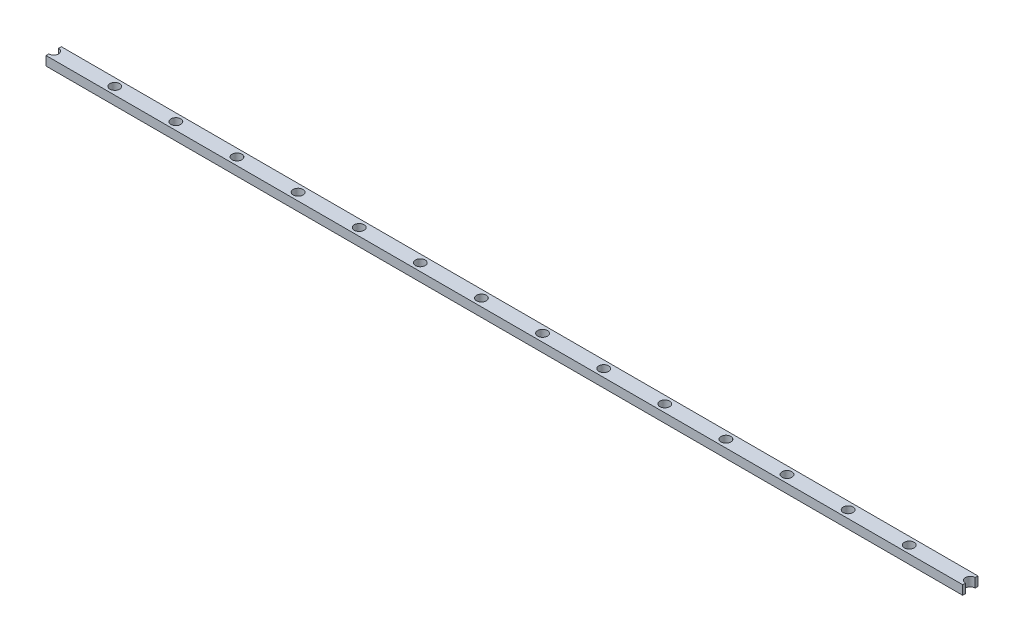
SolidWorks part; units mm, degrees
ref_plane "Front Plane" through (0, 0, 0) normal (0, 0, 1) x (1, 0, 0)
ref_plane "Top Plane" through (0, 0, 0) normal (0, 1, 0) x (1, 0, 0)
ref_plane "Right Plane" through (0, 0, 0) normal (1, 0, 0) x (0, 0, -1)
sketch "Sketch1" plane through (0, 0, 0) normal (0, 1, 0) x (1, 0, 0)
  line L1 (0, 0) -> (300, 0)
  line L2 (0, 0) -> (0, -5)
  line L3 (0, -5) -> (300, -5)
  line L4 (300, 0) -> (300, -5)
  line L5 (150, -5) -> (150, 0) construction
  line L6 (0, -2.5) -> (300, -2.5) construction
  point P188 (150, -2.5)
  dimension "D1" = 5
  dimension "D2" = 300
extrude "Boss-Extrude1" add sketch "Sketch1" along normal blind 3
sketch "Sketch2" plane through (0, 3, 0) normal (0, 1, 0) x (1, 0, 0)
  line L0 (0, 0) -> (0, -5) construction
  circle A0 centre (0, -2.5) radius 1.6
  circle A1 centre (20, -2.5) radius 1.6
  circle A2 centre (40, -2.5) radius 1.6
  circle A3 centre (60, -2.5) radius 1.6
  circle A4 centre (80, -2.5) radius 1.6
  circle A5 centre (100, -2.5) radius 1.6
  circle A6 centre (120, -2.5) radius 1.6
  circle A7 centre (140, -2.5) radius 1.6
  circle A8 centre (160, -2.5) radius 1.6
  circle A9 centre (180, -2.5) radius 1.6
  circle A10 centre (200, -2.5) radius 1.6
  circle A11 centre (220, -2.5) radius 1.6
  circle A12 centre (240, -2.5) radius 1.6
  circle A13 centre (260, -2.5) radius 1.6
  circle A14 centre (280, -2.5) radius 1.6
  circle A15 centre (300, -2.5) radius 1.6
  circle A16 centre (320, -2.5) radius 1.6
  circle A17 centre (340, -2.5) radius 1.6
  circle A18 centre (360, -2.5) radius 1.6
  circle A19 centre (380, -2.5) radius 1.6
  circle A20 centre (400, -2.5) radius 1.6
  circle A21 centre (420, -2.5) radius 1.6
  circle A22 centre (440, -2.5) radius 1.6
  circle A23 centre (460, -2.5) radius 1.6
  circle A24 centre (480, -2.5) radius 1.6
  circle A25 centre (500, -2.5) radius 1.6
  circle A26 centre (520, -2.5) radius 1.6
  circle A27 centre (540, -2.5) radius 1.6
  circle A28 centre (560, -2.5) radius 1.6
  circle A29 centre (580, -2.5) radius 1.6
  circle A30 centre (600, -2.5) radius 1.6
  circle A31 centre (620, -2.5) radius 1.6
  circle A32 centre (640, -2.5) radius 1.6
  circle A33 centre (660, -2.5) radius 1.6
  circle A34 centre (680, -2.5) radius 1.6
  circle A35 centre (700, -2.5) radius 1.6
  circle A36 centre (720, -2.5) radius 1.6
  circle A37 centre (740, -2.5) radius 1.6
  circle A38 centre (760, -2.5) radius 1.6
  circle A39 centre (780, -2.5) radius 1.6
  circle A40 centre (800, -2.5) radius 1.6
  circle A41 centre (820, -2.5) radius 1.6
  circle A42 centre (840, -2.5) radius 1.6
  circle A43 centre (860, -2.5) radius 1.6
  circle A44 centre (880, -2.5) radius 1.6
  circle A45 centre (900, -2.5) radius 1.6
  circle A46 centre (920, -2.5) radius 1.6
  circle A47 centre (940, -2.5) radius 1.6
  circle A48 centre (960, -2.5) radius 1.6
  circle A49 centre (980, -2.5) radius 1.6
  circle A50 centre (1000, -2.5) radius 1.6
  circle A51 centre (1020, -2.5) radius 1.6
  circle A52 centre (1040, -2.5) radius 1.6
  circle A53 centre (1060, -2.5) radius 1.6
  circle A54 centre (1080, -2.5) radius 1.6
  circle A55 centre (1100, -2.5) radius 1.6
  circle A56 centre (1120, -2.5) radius 1.6
  circle A57 centre (1140, -2.5) radius 1.6
  circle A58 centre (1160, -2.5) radius 1.6
  circle A59 centre (1180, -2.5) radius 1.6
  circle A60 centre (1200, -2.5) radius 1.6
  circle A61 centre (1220, -2.5) radius 1.6
  circle A62 centre (1240, -2.5) radius 1.6
  circle A63 centre (1260, -2.5) radius 1.6
  circle A64 centre (1280, -2.5) radius 1.6
  circle A65 centre (1300, -2.5) radius 1.6
  circle A66 centre (1320, -2.5) radius 1.6
  circle A67 centre (1340, -2.5) radius 1.6
  circle A68 centre (1360, -2.5) radius 1.6
  circle A69 centre (1380, -2.5) radius 1.6
  circle A70 centre (1400, -2.5) radius 1.6
  circle A71 centre (1420, -2.5) radius 1.6
  circle A72 centre (1440, -2.5) radius 1.6
  circle A73 centre (1460, -2.5) radius 1.6
  circle A74 centre (1480, -2.5) radius 1.6
  circle A75 centre (1500, -2.5) radius 1.6
  circle A76 centre (1520, -2.5) radius 1.6
  circle A77 centre (1540, -2.5) radius 1.6
  circle A78 centre (1560, -2.5) radius 1.6
  circle A79 centre (1580, -2.5) radius 1.6
  circle A80 centre (1600, -2.5) radius 1.6
  circle A81 centre (1620, -2.5) radius 1.6
  circle A82 centre (1640, -2.5) radius 1.6
  circle A83 centre (1660, -2.5) radius 1.6
  circle A84 centre (1680, -2.5) radius 1.6
  circle A85 centre (1700, -2.5) radius 1.6
  circle A86 centre (1720, -2.5) radius 1.6
  circle A87 centre (1740, -2.5) radius 1.6
  circle A88 centre (1760, -2.5) radius 1.6
  circle A89 centre (1780, -2.5) radius 1.6
  circle A90 centre (1800, -2.5) radius 1.6
  circle A91 centre (1820, -2.5) radius 1.6
  circle A92 centre (1840, -2.5) radius 1.6
  circle A93 centre (1860, -2.5) radius 1.6
  circle A94 centre (1880, -2.5) radius 1.6
  circle A95 centre (1900, -2.5) radius 1.6
  circle A96 centre (1920, -2.5) radius 1.6
  circle A97 centre (1940, -2.5) radius 1.6
  circle A98 centre (1960, -2.5) radius 1.6
  circle A99 centre (1980, -2.5) radius 1.6
  dimension "D1" = 3.2
  dimension "D2" = 20
extrude "Cut-Extrude1" cut sketch "Sketch2" against normal blind 3
equation "\"AXLE_LENTGH\"=29.0854"
